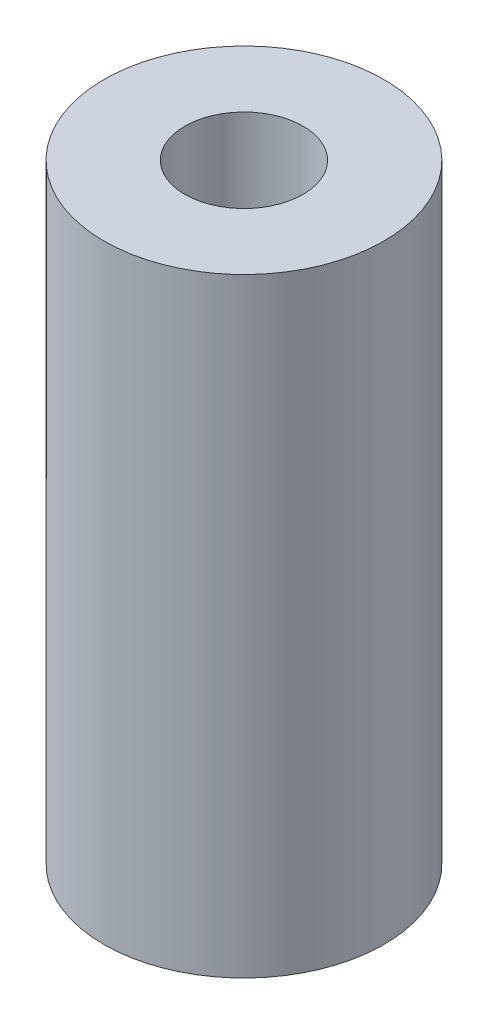
SolidWorks part; units mm, degrees
ref_plane "Front Plane" through (0, 0, 0) normal (0, 0, 1) x (1, 0, 0)
ref_plane "Top Plane" through (0, 0, 0) normal (0, 1, 0) x (1, 0, 0)
ref_plane "Right Plane" through (0, 0, 0) normal (1, 0, 0) x (0, 0, -1)
sketch "Sketch1" plane through (0, 0, 0) normal (0, 1, 0) x (1, 0, 0)
  line L0 (-9.5309, 7.008) -> (9.5309, -7.008) construction
  circle A0 centre (0, 0) radius 5
  circle A1 centre (0, 0) radius 11.83
  dimension "D1" = 10
extrude "Boss-Extrude1" add sketch "Sketch1" along normal blind 45.5 and the other way blind 6
